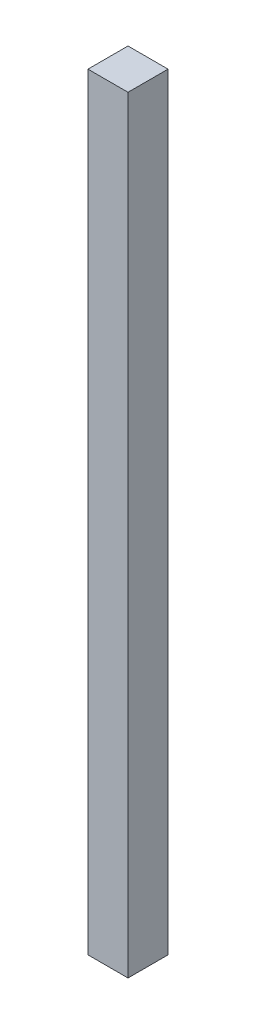
SolidWorks part; units mm, degrees
ref_plane "Front Plane" through (0, 0, 0) normal (0, 0, 1) x (1, 0, 0)
ref_plane "Top Plane" through (0, 0, 0) normal (0, 1, 0) x (1, 0, 0)
ref_plane "Right Plane" through (0, 0, 0) normal (1, 0, 0) x (0, 0, -1)
sketch "Sketch1" plane through (0, 0, 0) normal (0, 1, 0) x (1, 0, 0)
  line L1 (0, 0) -> (25.4, 0)
  line L2 (0, 0) -> (0, 25.4)
  line L3 (0, 25.4) -> (25.4, 25.4)
  line L4 (25.4, 0) -> (25.4, 25.4)
  dimension "D1" = 25.4
  dimension "D2" = 25.4
extrude "Boss-Extrude1" add sketch "Sketch1" along normal blind 486.41
